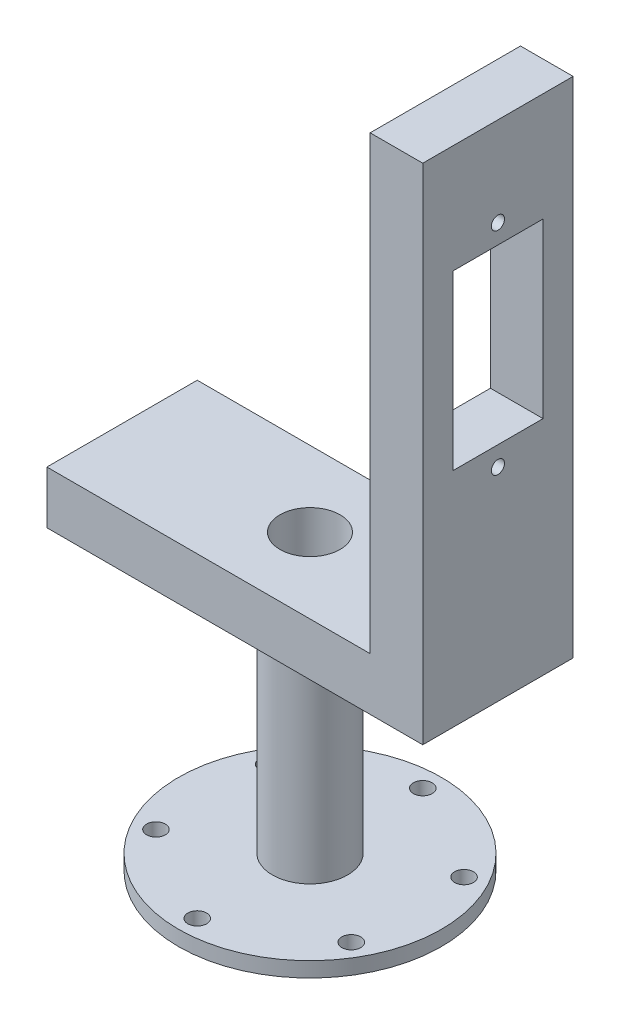
SolidWorks part; units mm, degrees
ref_plane "Front Plane" through (0, 0, 0) normal (0, 0, 1) x (1, 0, 0)
ref_plane "Top Plane" through (0, 0, 0) normal (0, 1, 0) x (1, 0, 0)
ref_plane "Right Plane" through (0, 0, 0) normal (1, 0, 0) x (0, 0, -1)
sketch "Sketch1" plane through (0, 0, 0) normal (0, 1, 0) x (1, 0, 0)
  circle A0 centre (0, 0) radius 17.5
extrude "Boss-Extrude1" add sketch "Sketch1" along normal blind 2
sketch "Sketch2" plane through (0, 2, 0) normal (0, 1, 0) x (1, 0, 0)
  circle A0 centre (0, 15) radius 1.25
  dimension "D1" = 15
extrude "Cut-Extrude1" cut sketch "Sketch2" against normal blind 5
pattern_circular "CirPattern1" count 6 every 60 about axis through (0, 0, 0) along (0, 1, 0) of "Cut-Extrude1"
sketch "Sketch3" plane through (0, 2, 0) normal (0, 1, 0) x (1, 0, 0)
  circle A0 centre (0, 0) radius 5
extrude "Boss-Extrude2" add sketch "Sketch3" along normal blind 30
sketch "Sketch4" plane through (0, 32, 0) normal (0, 1, 0) x (1, 0, 0)
  line L1 (-25, 10) -> (25, 10)
  line L2 (-25, 10) -> (-25, -10)
  line L3 (-25, -10) -> (25, -10)
  line L4 (25, 10) -> (25, -10)
  dimension "D1" = 20
  dimension "D2" = 50
  dimension "D4" = 10
extrude "Boss-Extrude3" add sketch "Sketch4" along normal blind 7
sketch "Sketch5" plane through (0, 39, 0) normal (0, 1, 0) x (1, 0, 0)
  line L0 (25, 10) -> (-25, 10) construction
  line L1 (18, 10) -> (25, 10)
  line L2 (18, 10) -> (18, -10)
  line L3 (18, -10) -> (25, -10)
  line L4 (25, 10) -> (25, -10)
  point P7 (18, 0)
  dimension "D1" = 18
extrude "Boss-Extrude4" add sketch "Sketch5" along normal blind 60
sketch "Sketch6" plane through (18, 0, 0) normal (-1, 0, 0) x (0, 0, 1)
  circle A0 centre (0, 87.15) radius 0.875
  circle A1 centre (0, 59) radius 0.875
  dimension "D1" = 2
  dimension "D2" = 28.15
extrude "Cut-Extrude2" cut sketch "Sketch6" against normal blind 7
sketch "Sketch7" plane through (18, 0, 0) normal (-1, 0, 0) x (0, 0, 1)
  line L1 (-6, 84.575) -> (6, 84.575)
  line L2 (-6, 84.575) -> (-6, 61.575)
  line L3 (-6, 61.575) -> (6, 61.575)
  line L4 (6, 84.575) -> (6, 61.575)
  circle A0 centre (0, 87.15) radius 0.875 construction
  dimension "D3" = 2.575
  dimension "D4" = 6
  dimension "D1" = 23
  dimension "D2" = 12
extrude "Cut-Extrude3" cut sketch "Sketch7" against normal blind 7
sketch "Sketch8" plane through (0, 32, 0) normal (0, -1, 0) x (-1, 0, 0)
  circle A0 centre (0, 0) radius 4
extrude "Cut-Extrude4" cut sketch "Sketch8" against normal blind 7 and the other way blind 32
